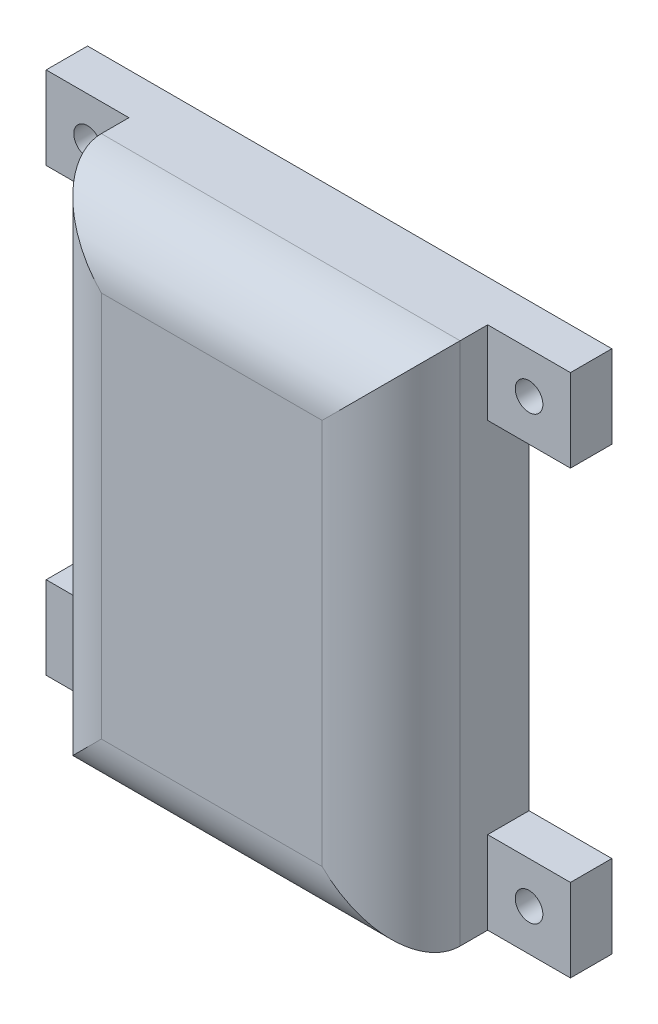
SolidWorks part; units mm, degrees
ref_plane "正面" through (0, 0, 0) normal (0, 0, 1) x (1, 0, 0)
ref_plane "平面" through (0, 0, 0) normal (0, 1, 0) x (1, 0, 0)
ref_plane "右側面" through (0, 0, 0) normal (1, 0, 0) x (0, 0, -1)
sketch "ｽｹｯﾁ1" plane through (0, 0, 0) normal (0, 0, 1) x (1, 0, 0)
  line L1 (13, -19) -> (-13, -19)
  line L2 (13, -19) -> (13, 19)
  line L3 (13, 19) -> (-13, 19)
  line L4 (-13, -19) -> (-13, 19)
  line L5 (13, -19) -> (-13, 19) construction
  line L6 (13, 19) -> (-13, -19) construction
  point P0 (0, 0)
  dimension "D1" = 38
  dimension "D2" = 26
extrude "ﾎﾞｽ - 押し出し1" add sketch "ｽｹｯﾁ1" along normal blind 10
sketch "ｽｹｯﾁ2" plane through (0, 0, 0) normal (0, 0, 1) x (1, 0, 0)
  line L1 (11, -17) -> (-11, -17)
  line L2 (11, -17) -> (11, 17)
  line L3 (11, 17) -> (-11, 17)
  line L4 (-11, -17) -> (-11, 17)
  line L5 (11, -17) -> (-11, 17) construction
  line L6 (11, 17) -> (-11, -17) construction
  point P0 (0, 0)
  dimension "D1" = 22
  dimension "D2" = 34
extrude "ｶｯﾄ - 押し出し1" cut sketch "ｽｹｯﾁ2" along normal blind 8
sketch "ｽｹｯﾁ3" plane through (0, 0, 0) normal (0, 0, 1) x (1, 0, 0)
  line L0 (13, 19) -> (-13, 19) construction
  line L1 (-0.8522, 2) -> (1.1478, 2)
  line L2 (-0.8522, 2) -> (-0.8522, 9)
  line L3 (-0.8522, 9) -> (1.1478, 9)
  line L4 (1.1478, 2) -> (1.1478, 9)
  line L5 (-0.8522, 2) -> (1.1478, 9) construction
  line L6 (-0.8522, 9) -> (1.1478, 2) construction
  point P0 (0.1478, 5.5)
  dimension "D1" = 7
  dimension "D2" = 2
  dimension "D3" = 10
sketch "ｽｹｯﾁ4" plane through (0, 0, 0) normal (0, 0, 1) x (1, 0, 0)
  line L0 (13, -19) -> (13, 19) construction
  line L1 (13, 19) -> (19, 19)
  line L2 (13, 19) -> (13, 13)
  line L3 (13, 13) -> (19, 13)
  line L4 (19, 19) -> (19, 13)
  line L5 (13, -19) -> (19, -19)
  line L6 (13, -19) -> (13, -13)
  line L7 (13, -13) -> (19, -13)
  line L8 (19, -19) -> (19, -13)
  line L9 (-13, -19) -> (13, -19) construction
  line L10 (-13, -19) -> (-19, -19)
  line L11 (-13, -19) -> (-13, -13)
  line L12 (-13, -13) -> (-19, -13)
  line L13 (-19, -19) -> (-19, -13)
  line L14 (-13, 19) -> (-19, 19)
  line L15 (-13, 19) -> (-13, 13)
  line L16 (-13, 13) -> (-19, 13)
  line L17 (-19, 19) -> (-19, 13)
  dimension "D1" = 6
  dimension "D2" = 6
  dimension "D3" = 6
  dimension "D4" = 6
  dimension "D5" = 6
  dimension "D6" = 6
  dimension "D7" = 6
  dimension "D8" = 6
  dimension "D9" = 0
extrude "ﾎﾞｽ - 押し出し2" add sketch "ｽｹｯﾁ4" along normal blind 3
sketch "ｽｹｯﾁ5" plane through (0, 0, 0) normal (0, 0, 1) x (1, 0, 0)
  line L0 (-13, 19) -> (-19, 19) construction
  line L1 (-19, 19) -> (-19, 13) construction
  line L2 (-13, -13) -> (-19, -13) construction
  line L3 (19, -19) -> (19, -13) construction
  line L4 (-19, -13) -> (-19, -19) construction
  line L5 (19, -13) -> (13, -13) construction
  line L6 (19, 13) -> (19, 19) construction
  line L7 (19, 19) -> (13, 19) construction
  circle A0 centre (-16, 16) radius 1
  circle A1 centre (-16, -16) radius 1
  circle A2 centre (16, -16) radius 1
  circle A3 centre (16, 16) radius 1
  dimension "D1" = 3
  dimension "D2" = 3
  dimension "D3" = 3
  dimension "D4" = 2
  dimension "D5" = 2
  dimension "D6" = 3
  dimension "D7" = 2
  dimension "D8" = 2
  dimension "D9" = 3
  dimension "D10" = 3
  dimension "D11" = 3
  dimension "D12" = 3
extrude "ｶｯﾄ - 押し出し4" cut sketch "ｽｹｯﾁ5" along normal through all
fillet "ﾌｨﾚｯﾄ1" radius 5 4 edges at (0, 19, 10) (0, -19, 10) (13, 0, 10) (-13, 0, 10)
